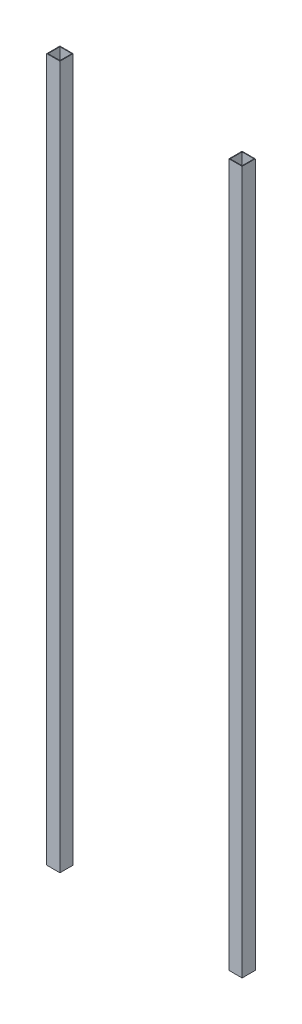
SolidWorks part; units mm, degrees
ref_plane "Front Plane" through (0, 0, 0) normal (0, 0, 1) x (1, 0, 0)
ref_plane "Top Plane" through (0, 0, 0) normal (0, 1, 0) x (1, 0, 0)
ref_plane "Right Plane" through (0, 0, 0) normal (1, 0, 0) x (0, 0, -1)
sketch "Sketch1" plane through (0, 0, 0) normal (0, 1, 0) x (1, 0, 0)
  line L0 (32.258, 0) -> (0, 32.258) construction
  line L1 (0, 0) -> (32.258, 0)
  line L2 (0, 0) -> (0, 32.258)
  line L3 (0, 32.258) -> (32.258, 32.258)
  line L4 (32.258, 0) -> (32.258, 32.258)
  line L5 (33.909, -1.651) -> (33.909, 33.909)
  line L6 (-1.651, 33.909) -> (33.909, 33.909)
  line L7 (-1.651, -1.651) -> (-1.651, 33.909)
  line L8 (-1.651, -1.651) -> (33.909, -1.651)
  line L9 (16.129, 16.129) -> (508.254, 16.129) construction
  line L11 (490.474, -1.651) -> (526.034, -1.651)
  line L12 (490.474, -1.651) -> (490.474, 33.909)
  line L13 (490.474, 33.909) -> (526.034, 33.909)
  line L14 (526.034, -1.651) -> (526.034, 33.909)
  line L15 (490.474, -1.651) -> (526.034, 33.909) construction
  line L16 (490.474, 33.909) -> (526.034, -1.651) construction
  line L17 (492.125, 0) -> (524.383, 0)
  line L18 (492.125, 0) -> (492.125, 32.258)
  line L19 (492.125, 32.258) -> (524.383, 32.258)
  line L20 (524.383, 0) -> (524.383, 32.258)
  line L21 (492.125, 0) -> (524.383, 32.258) construction
  line L22 (492.125, 32.258) -> (524.383, 0) construction
  dimension "D1" = 32.258
  dimension "D2" = 1.651
  dimension "D3" = 492.125
extrude "Boss-Extrude1" add sketch "Sketch1" along normal blind 1898.65
